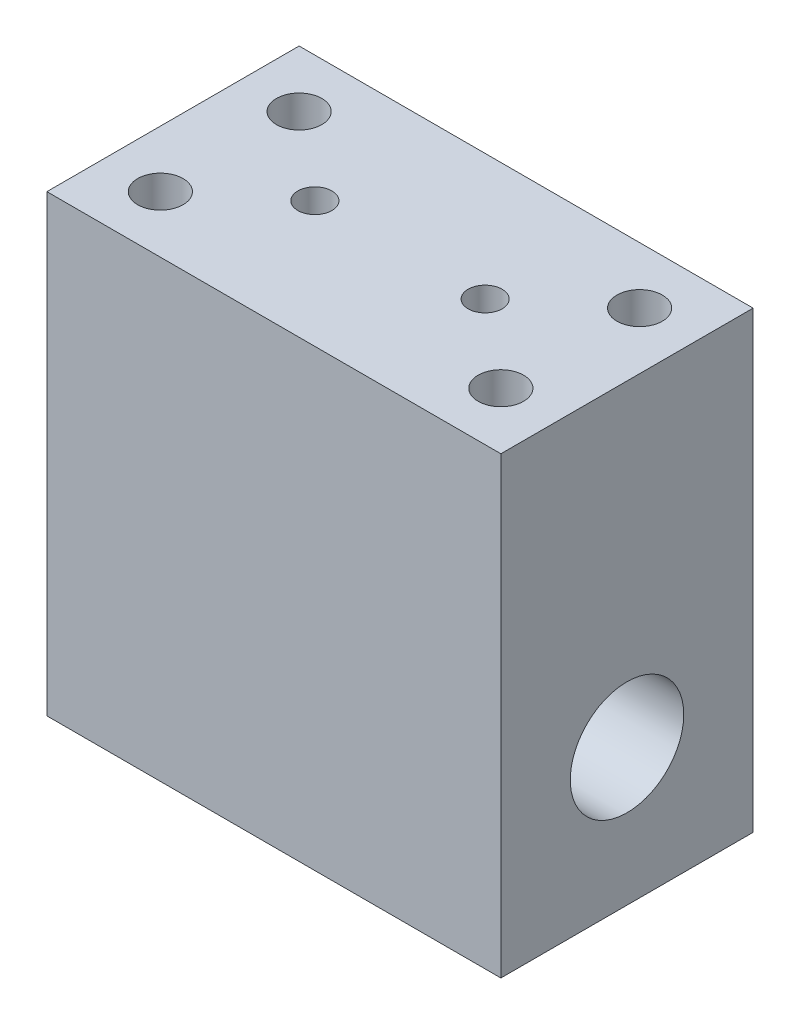
SolidWorks part; units mm, degrees
material "AISI 316 Chapa de aço inoxidável (SS)"
ref_plane "Plano frontal" through (0, 0, 0) normal (0, 0, 1) x (1, 0, 0)
ref_plane "Plano superior" through (0, 0, 0) normal (0, 1, 0) x (1, 0, 0)
ref_plane "Plano direito" through (0, 0, 0) normal (1, 0, 0) x (0, 0, -1)
sketch "Esboço2" plane through (0, 0, 0) normal (0, 0, 1) x (1, 0, 0)
  line L1 (-40, -40) -> (40, -40)
  line L2 (-40, -40) -> (-40, 40)
  line L3 (-40, 40) -> (40, 40)
  line L4 (40, -40) -> (40, 40)
  line L5 (-40, -40) -> (40, 40) construction
  line L6 (-40, 40) -> (40, -40) construction
  point P0 (0, 0)
  dimension "D1" = 80
  dimension "D2" = 80
extrude "Ressalto-extrusão2" add sketch "Esboço2" along normal mid plane 44.45
sketch "Esboço10" plane through (0, 40, 0) normal (0, 1, 0) x (1, 0, 0)
  line L3 (40, -22.225) -> (-40, -22.225) construction
  line L4 (40, -22.225) -> (40, 22.225) construction
  line L5 (40, 22.225) -> (-40, 22.225) construction
  line L6 (-40, -22.225) -> (-40, 22.225) construction
  circle A0 centre (30, -12.225) radius 4
  circle A1 centre (30, 12.225) radius 4
  circle A2 centre (-30, -12.225) radius 4
  circle A3 centre (-30, 12.225) radius 4
  circle A4 centre (15, 0) radius 3
  circle A5 centre (-15, 0) radius 3
  point P15 (0, 0)
  dimension "D1" = 30
  dimension "D2" = 15
  dimension "D5" = 8
  dimension "D3" = 8
  dimension "D4" = 8
  dimension "D6" = 8
  dimension "D7" = 10
  dimension "D8" = 10
  dimension "D9" = 10
  dimension "D10" = 10
  dimension "D11" = 10
  dimension "D12" = 10
  dimension "D13" = 10
  dimension "D14" = 10
  dimension "D15" = 6
  dimension "D16" = 6
extrude "Corte-extrusão5" cut sketch "Esboço10" against normal blind 30
cosmetic thread "Representação de rosca1" parameters "D2"=10
cosmetic thread "Representação de rosca2" parameters "D2"=10
cosmetic thread "Representação de rosca3" parameters "D2"=10
cosmetic thread "Representação de rosca4" parameters "D2"=10
sketch "Esboço12" plane through (40, 0, 0) normal (1, 0, 0) x (0, 0, -1)
  line L1 (-22.225, 40) -> (22.225, 40) construction
  circle A0 centre (0, -15.9) radius 10
  dimension "D1" = 20
  dimension "D2" = 55.9
extrude "Corte-extrusão7" cut sketch "Esboço12" against normal through all
thread "Rosca1" pitch 1.25 start angle 0, offset 0, length 0, pitch 1.25, diameter 8
ref_plane "Plano1" through (26, 40, 12.225) normal (0, 0, 1) x (-1, 0, 0)
sketch "Perfil da rosca1" plane through (26, 40, 12.225) normal (0, 0, 1) x (-1, 0, 0)
  line L0 (0, 0) -> (0, 1.25) construction
  line L11 (0, 0) -> (0, 1.0937)
  line L12 (0, 1.0937) -> (-0.6766, 0.7031)
  line L13 (-0.6766, 0.7031) -> (-0.6766, 0.3906)
  line L15 (-0.6766, 0.3906) -> (0, 0)
  line L17 (-0.6766, 0.5469) -> (0, 0.5469) construction
  point P2 (0, 0)
  dimension "Pitch" = 1.25
  dimension "Profile_Angle" = 60
  dimension "Profile_Land" = 0.3125
  dimension "Profile_Height" = 0.6766
thread "Rosca2" pitch 1.25 start angle 0, offset 0, length 0, pitch 1.25, diameter 8
ref_plane "Plano2" through (26, 40, -12.225) normal (0, 0, 1) x (-1, 0, 0)
sketch "Perfil da rosca2" plane through (26, 40, -12.225) normal (0, 0, 1) x (-1, 0, 0)
  line L0 (0, 0) -> (0, 1.25) construction
  line L11 (0, 0) -> (0, 1.0937)
  line L12 (0, 1.0937) -> (-0.6766, 0.7031)
  line L13 (-0.6766, 0.7031) -> (-0.6766, 0.3906)
  line L15 (-0.6766, 0.3906) -> (0, 0)
  line L17 (-0.6766, 0.5469) -> (0, 0.5469) construction
  point P2 (0, 0)
  dimension "Pitch" = 1.25
  dimension "Profile_Angle" = 60
  dimension "Profile_Land" = 0.3125
  dimension "Profile_Height" = 0.6766
thread "Rosca3" pitch 1.25 start angle 0, offset 0, length 0, pitch 1.25, diameter 8
ref_plane "Plano3" through (-34, 40, 12.225) normal (0, 0, 1) x (-1, 0, 0)
sketch "Perfil da rosca3" plane through (-34, 40, 12.225) normal (0, 0, 1) x (-1, 0, 0)
  line L0 (0, 0) -> (0, 1.25) construction
  line L11 (0, 0) -> (0, 1.0937)
  line L12 (0, 1.0937) -> (-0.6766, 0.7031)
  line L13 (-0.6766, 0.7031) -> (-0.6766, 0.3906)
  line L15 (-0.6766, 0.3906) -> (0, 0)
  line L17 (-0.6766, 0.5469) -> (0, 0.5469) construction
  point P2 (0, 0)
  dimension "Pitch" = 1.25
  dimension "Profile_Angle" = 60
  dimension "Profile_Land" = 0.3125
  dimension "Profile_Height" = 0.6766
thread "Rosca4" pitch 1.25 start angle 0, offset 0, length 0, pitch 1.25, diameter 8
ref_plane "Plano4" through (-34, 40, -12.225) normal (0, 0, 1) x (-1, 0, 0)
sketch "Perfil da rosca4" plane through (-34, 40, -12.225) normal (0, 0, 1) x (-1, 0, 0)
  line L0 (0, 0) -> (0, 1.25) construction
  line L11 (0, 0) -> (0, 1.0937)
  line L12 (0, 1.0937) -> (-0.6766, 0.7031)
  line L13 (-0.6766, 0.7031) -> (-0.6766, 0.3906)
  line L15 (-0.6766, 0.3906) -> (0, 0)
  line L17 (-0.6766, 0.5469) -> (0, 0.5469) construction
  point P2 (0, 0)
  dimension "Pitch" = 1.25
  dimension "Profile_Angle" = 60
  dimension "Profile_Land" = 0.3125
  dimension "Profile_Height" = 0.6766
